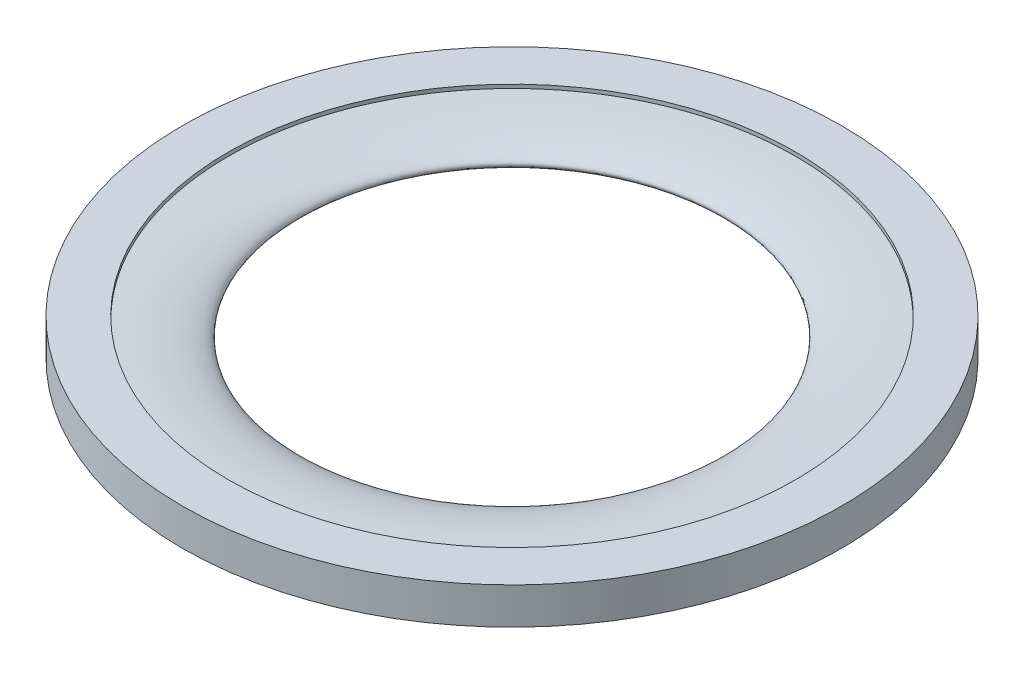
SolidWorks part; units mm, degrees
ref_plane "Front Plane" through (0, 0, 0) normal (0, 0, 1) x (1, 0, 0)
ref_plane "Top Plane" through (0, 0, 0) normal (0, 1, 0) x (1, 0, 0)
ref_plane "Right Plane" through (0, 0, 0) normal (1, 0, 0) x (0, 0, -1)
sketch "Sketch1" plane through (0, 0, 0) normal (0, 1, 0) x (1, 0, 0)
  circle A0 centre (0, 0) radius 9
  circle A1 centre (0, 0) radius 7.75
  dimension "D1" = 18
  dimension "D2" = 1.25
extrude "Boss-Extrude1" add sketch "Sketch1" along normal blind 1
sketch "Sketch3" plane through (0, 0, 0) normal (0, 0, 1) x (1, 0, 0)
  line L0 (0, 0) -> (-7.75, 0)
  line L1 (-9, 0) -> (9, 0) construction
  line L2 (-7.75, 0) -> (7.75, 0) construction
  line L3 (-7.75, 0) -> (-7.75, 1)
  line L4 (7.75, 1) -> (-7.75, 1) construction
  line L5 (-7.75, 1) -> (-7.75, 0.5)
  line L6 (-7.75, 0.5) -> (-5.75, 0.5)
  line L7 (0, 0) -> (0, 0.75)
  ellipse E0 centre (-7.75, 0.5) end of major axis (-5.75, 0.5) minor radius 0.4 (-7.75, 0.1) -> (-7.75, 0.9) ccw
  dimension "D1" = 2
  dimension "D2" = 7.75
revolve "Revolve1" add sketch "Sketch3" angle 360 about L7
